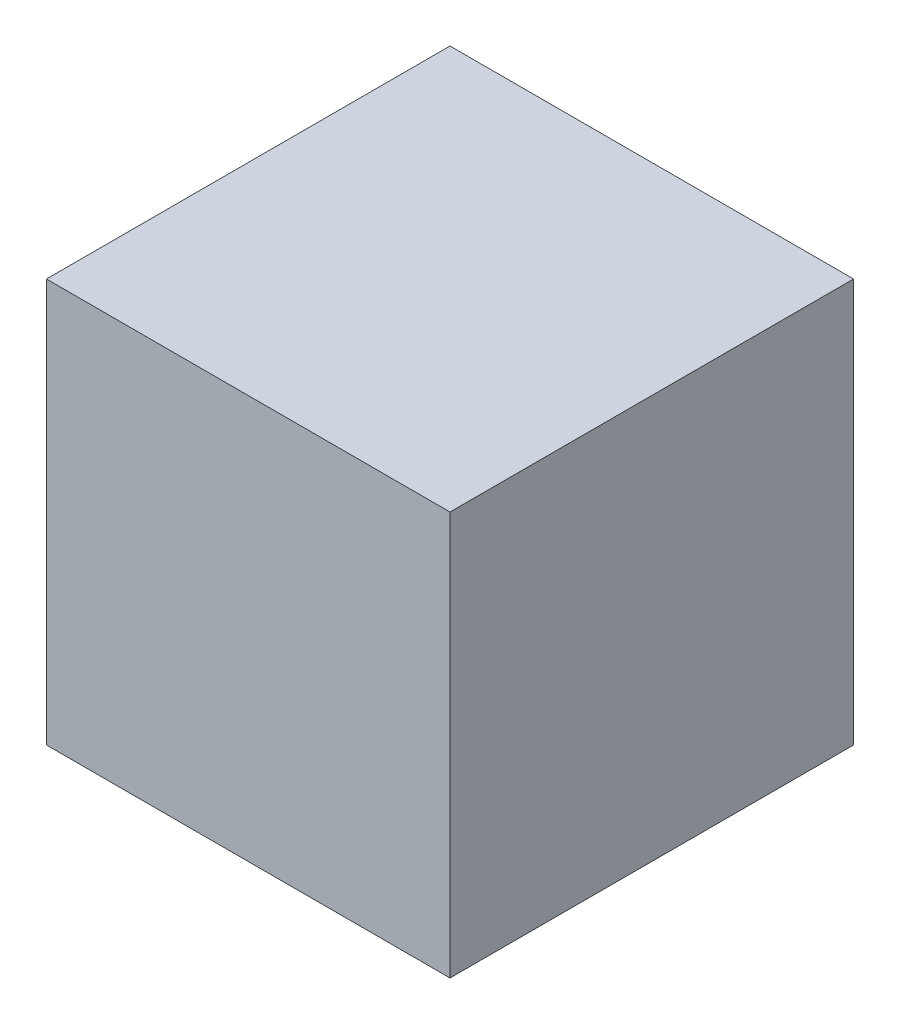
SolidWorks part; units mm, degrees
ref_plane "Front Plane" through (0, 0, 0) normal (0, 0, 1) x (1, 0, 0)
ref_plane "Top Plane" through (0, 0, 0) normal (0, 1, 0) x (1, 0, 0)
ref_plane "Right Plane" through (0, 0, 0) normal (1, 0, 0) x (0, 0, -1)
sketch "Sketch1" plane through (0, 0, 0) normal (0, 1, 0) x (1, 0, 0)
  line L1 (0, 0) -> (25, 0)
  line L2 (0, 0) -> (0, 25)
  line L3 (0, 25) -> (25, 25)
  line L4 (25, 0) -> (25, 25)
extrude "Boss-Extrude1" add sketch "Sketch1" along normal blind 25
sketch "Sketch2" plane through (0, 25, 0) normal (0, 1, 0) x (1, 0, 0)
